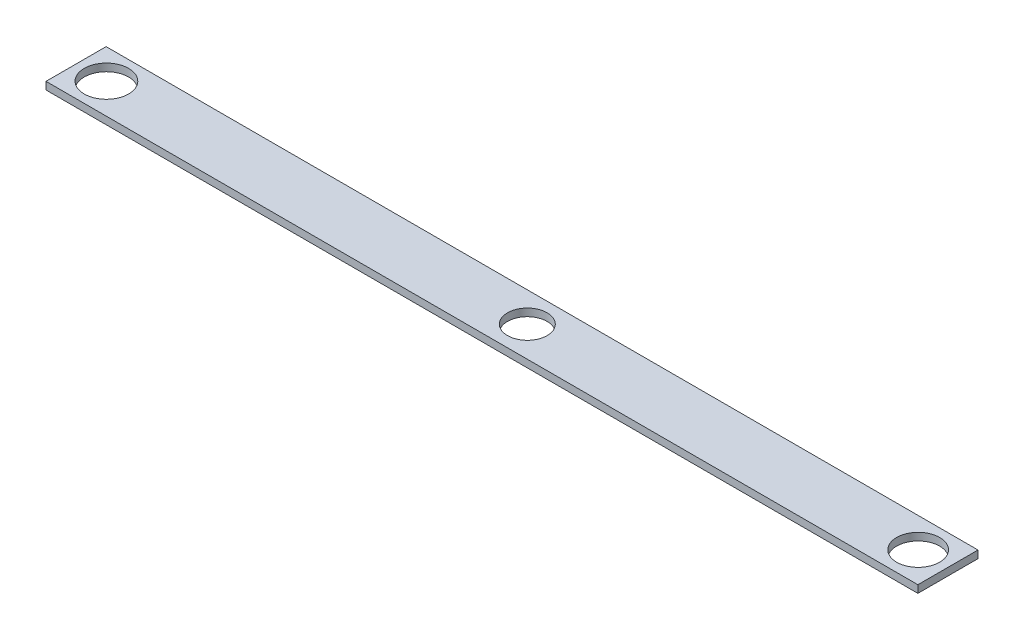
SolidWorks part; units mm, degrees
ref_plane "Front Plane" through (0, 0, 0) normal (0, 0, 1) x (1, 0, 0)
ref_plane "Top Plane" through (0, 0, 0) normal (0, 1, 0) x (1, 0, 0)
ref_plane "Right Plane" through (0, 0, 0) normal (1, 0, 0) x (0, 0, -1)
sketch "Sketch2" plane through (0, 0, 0) normal (0, 1, 0) x (1, 0, 0)
  line L0 (-88.9, 0) -> (82.55, 0) construction
  line L1 (-95.25, 6.2907) -> (88.9, 6.2907)
  line L2 (-95.25, 6.2907) -> (-95.25, -6.4093)
  line L3 (-95.25, -6.4093) -> (88.9, -6.4093)
  line L4 (88.9, 6.2907) -> (88.9, -6.4093)
  circle A0 centre (0, 0) radius 4.1812
  circle A1 centre (82.55, 0) radius 4.5365
  circle A2 centre (-88.9, 0) radius 4.6888
  point P11 (0, 0)
  dimension "D1" = 6.35
  dimension "D2" = 88.9
  dimension "D3" = 6.35
  dimension "D4" = 82.55
  dimension "D5" = 12.7
extrude "Boss-Extrude1" add sketch "Sketch2" along normal blind 1.5875
